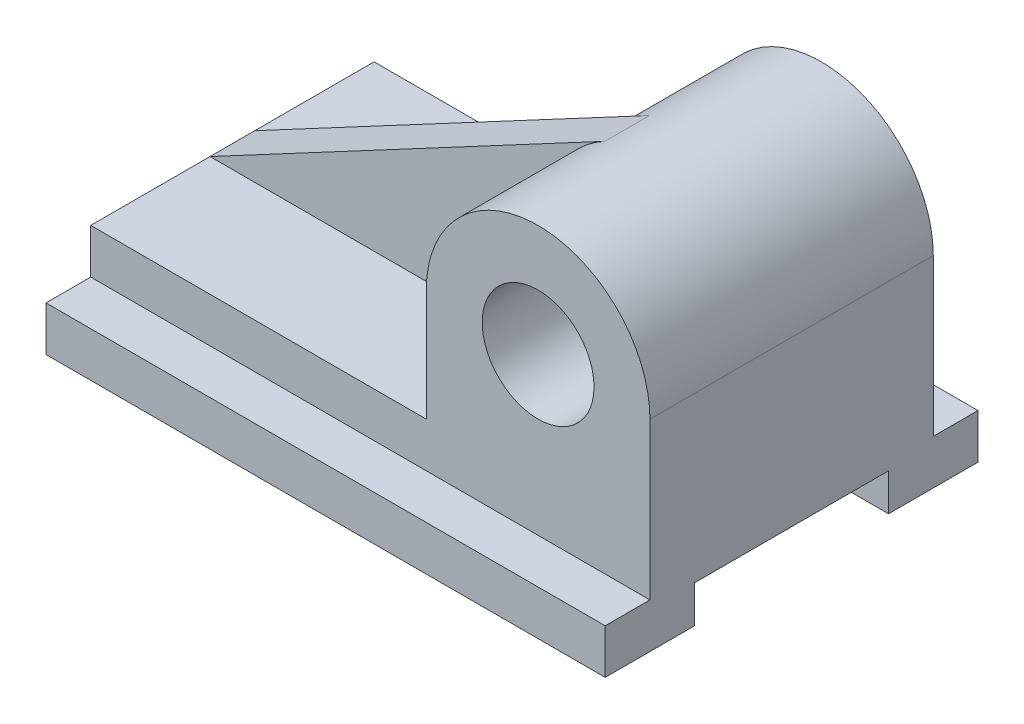
SolidWorks part; units mm, degrees
ref_plane "Front Plane" through (0, 0, 0) normal (0, 0, 1) x (1, 0, 0)
ref_plane "Top Plane" through (0, 0, 0) normal (0, 1, 0) x (1, 0, 0)
ref_plane "Right Plane" through (0, 0, 0) normal (1, 0, 0) x (0, 0, -1)
sketch "Sketch2" plane through (0, 0, 0) normal (0, 0, 1) x (1, 0, 0)
  line L1 (-30, 0) -> (30, 0)
  line L2 (-30, 0) -> (-30, -54)
  line L3 (-30, -54) -> (30, -54)
  line L4 (30, 0) -> (30, -54)
  line L5 (-30, -54) -> (-120, -54)
  line L6 (-30, -54) -> (-30, -30)
  line L7 (-30, -30) -> (-120, -30)
  line L8 (-120, -54) -> (-120, -30)
  circle A0 centre (0, 0) radius 30
  circle A1 centre (0, 0) radius 15
extrude "Boss-Extrude1" add sketch "Sketch2" along normal blind 76 contours A0 L2 L3 L4 | L8 L5 L2 L7 | A1 L1 A0 | A1 L1 A0
sketch "Sketch3" plane through (0, 0, 76) normal (0, 0, 1) x (1, 0, 0)
  line L0 (30, 0) -> (30, -54) construction
  line L1 (-120, -54) -> (30, -54)
  line L2 (-120, -54) -> (-120, -42)
  line L3 (-120, -42) -> (30, -42)
  line L4 (30, -54) -> (30, -42)
extrude "Boss-Extrude2" add sketch "Sketch3" along normal blind 12
sketch "Sketch4" plane through (0, 0, 0) normal (0, 0, -1) x (-1, 0, 0)
  line L0 (120, -54) -> (120, -30) construction
  line L1 (-30, -54) -> (120, -54)
  line L2 (-30, -54) -> (-30, -42)
  line L3 (-30, -42) -> (120, -42)
  line L4 (120, -54) -> (120, -42)
extrude "Boss-Extrude3" add sketch "Sketch4" along normal blind 12
sketch "Sketch5" plane through (0, -54, 0) normal (0, -1, 0) x (-1, 0, 0)
  line L3 (120, -12) -> (-30, -12)
  line L4 (120, -64) -> (-30, -64)
  line L5 (120, -64) -> (-30, -64)
  line L6 (120, -64) -> (120, -12)
  line L7 (120, -12) -> (-30, -12)
  line L8 (-30, -64) -> (-30, -12)
  line M1 (120, -88) -> (120, 12)
  line M3 (-30, 12) -> (-30, -88)
extrude "Cut-Extrude1" cut sketch "Sketch5" against normal blind 10 contours L4 L3 M1 M3
sketch "Sketch11" plane through (0, 0, 0) normal (0, 0, 1) x (1, 0, 0)
  line L0 (-120, -30) -> (-14.1176, 26.4706)
  line L1 (-30, 0) -> (-30, -30)
  line L2 (-30, -30) -> (-120, -30)
  arc A1 (30, 0) -> (-30, 0) centre (0, 0) ccw construction
  circle A2 centre (0, 0) radius 30
extrude "Boss-Extrude6" add sketch "Sketch11" along normal blind 44 contours A2 L0 L2 L1
sketch "Sketch13" plane through (0, 0, 0) normal (0, 0, 1) x (1, 0, 0)
  line L0 (-30, 0) -> (-30, -42)
  line L1 (-120, -42) -> (30, -42) construction
  line L2 (-120, -30) -> (-30, -30)
  line L3 (-14.1176, 26.4706) -> (-120, -30)
  circle A0 centre (0, 0) radius 30
extrude "Cut-Extrude2" cut sketch "Sketch13" along normal blind 32 contours A0 L3 L2 L0
